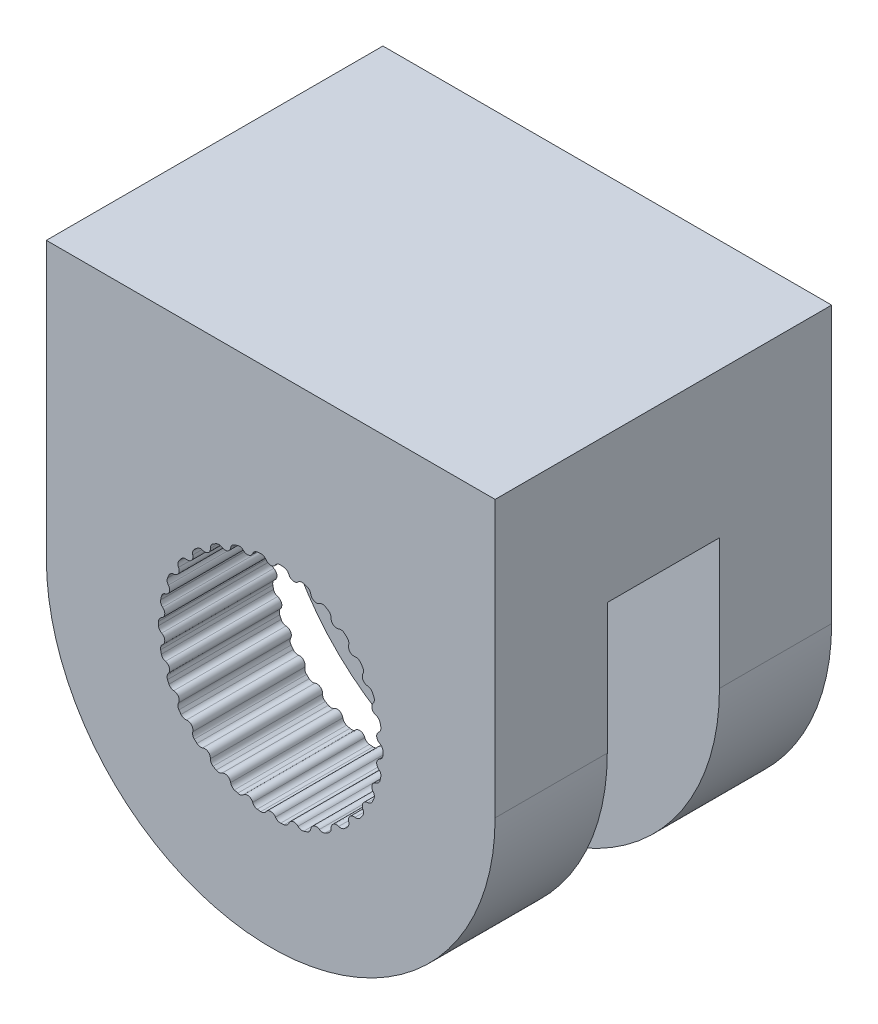
SolidWorks part; units mm, degrees
ref_plane "Front Plane" through (0, 0, 0) normal (0, 0, 1) x (1, 0, 0)
ref_plane "Top Plane" through (0, 0, 0) normal (0, 1, 0) x (1, 0, 0)
ref_plane "Right Plane" through (0, 0, 0) normal (1, 0, 0) x (0, 0, -1)
sketch "Sketch1" plane through (0, 0, 0) normal (0, 0, 1) x (1, 0, 0)
  line L0 (-51.514, -77.6376) -> (-11.514, -77.6376)
  line L1 (-51.514, -102.226) -> (-51.514, -77.6376)
  line L2 (-11.514, -102.226) -> (-11.514, -77.6376)
  arc A0 (-34.4531, -111.7843) -> (-34.7544, -111.6864) centre (-31.514, -102.226) cw
  arc A1 (-36.3762, -110.9643) -> (-36.6505, -110.806) centre (-31.514, -102.226) cw
  arc A2 (-38.0868, -109.7625) -> (-38.3221, -109.5505) centre (-31.514, -102.226) cw
  arc A3 (-39.51, -108.2312) -> (-39.6962, -107.975) centre (-31.514, -102.226) cw
  arc A4 (-40.5839, -106.4375) -> (-40.7127, -106.1482) centre (-31.514, -102.226) cw
  arc A5 (-41.2613, -104.4598) -> (-41.3272, -104.1499) centre (-31.514, -102.226) cw
  arc A6 (-41.5127, -102.3844) -> (-41.5127, -102.0676) centre (-31.514, -102.226) cw
  arc A7 (-41.3272, -100.302) -> (-41.2613, -99.9922) centre (-31.514, -102.226) cw
  arc A8 (-40.7127, -98.3038) -> (-40.5839, -98.0144) centre (-31.514, -102.226) cw
  arc A9 (-39.6962, -96.477) -> (-39.51, -96.2207) centre (-31.514, -102.226) cw
  arc A10 (-38.3221, -94.9014) -> (-38.0868, -94.6895) centre (-31.514, -102.226) cw
  arc A11 (-36.6505, -93.646) -> (-36.3762, -93.4876) centre (-31.514, -102.226) cw
  arc A12 (-34.7544, -92.7656) -> (-34.4531, -92.6677) centre (-31.514, -102.226) cw
  arc A13 (-32.7166, -92.2986) -> (-32.4016, -92.2655) centre (-31.514, -102.226) cw
  arc A14 (-30.6263, -92.2655) -> (-30.3113, -92.2986) centre (-31.514, -102.226) cw
  arc A15 (-28.5748, -92.6677) -> (-28.2736, -92.7656) centre (-31.514, -102.226) cw
  arc A16 (-26.6518, -93.4876) -> (-26.3775, -93.646) centre (-31.514, -102.226) cw
  arc A17 (-24.9412, -94.6895) -> (-24.7058, -94.9014) centre (-31.514, -102.226) cw
  arc A18 (-23.5179, -96.2207) -> (-23.3317, -96.477) centre (-31.514, -102.226) cw
  arc A19 (-22.4441, -98.0144) -> (-22.3153, -98.3038) centre (-31.514, -102.226) cw
  arc A20 (-21.7667, -99.9922) -> (-21.7008, -100.302) centre (-31.514, -102.226) cw
  arc A21 (-21.5152, -102.0676) -> (-21.5152, -102.3844) centre (-31.514, -102.226) cw
  arc A22 (-21.7008, -104.1499) -> (-21.7667, -104.4598) centre (-31.514, -102.226) cw
  arc A23 (-22.3153, -106.1482) -> (-22.4441, -106.4375) centre (-31.514, -102.226) cw
  arc A24 (-23.3317, -107.975) -> (-23.5179, -108.2312) centre (-31.514, -102.226) cw
  arc A25 (-24.7058, -109.5505) -> (-24.9412, -109.7625) centre (-31.514, -102.226) cw
  arc A26 (-26.3775, -110.806) -> (-26.6518, -110.9643) centre (-31.514, -102.226) cw
  arc A27 (-28.2736, -111.6864) -> (-28.5748, -111.7843) centre (-31.514, -102.226) cw
  arc A28 (-30.3113, -112.1534) -> (-30.6263, -112.1865) centre (-31.514, -102.226) cw
  arc A29 (-33.9496, -111.6569) -> (-33.1248, -111.8322) centre (-33.5931, -112.0075) cw
  arc A30 (-35.8572, -110.9444) -> (-35.0869, -111.2874) centre (-35.5813, -111.3614) cw
  arc A31 (-37.575, -109.8509) -> (-36.8928, -110.3466) centre (-37.3918, -110.3162) cw
  arc A32 (-39.0278, -108.4241) -> (-38.4636, -109.0508) centre (-38.9454, -108.9173) cw
  arc A33 (-40.1523, -106.7265) -> (-39.7307, -107.4568) centre (-40.1742, -107.226) cw
  arc A34 (-40.8992, -104.8321) -> (-40.6387, -105.6341) centre (-41.0245, -105.3162) cw
  arc A35 (-41.236, -102.8239) -> (-41.1479, -103.6625) centre (-41.4592, -103.2713) cw
  arc A36 (-41.1479, -100.7895) -> (-41.236, -101.6281) centre (-41.4592, -101.1807) cw
  arc A37 (-40.6387, -98.8179) -> (-40.8992, -99.6199) centre (-41.0245, -99.1358) cw
  arc A38 (-39.7307, -96.9952) -> (-40.1523, -97.7255) centre (-40.1742, -97.226) cw
  arc A39 (-38.4636, -95.4012) -> (-39.0278, -96.0278) centre (-38.9454, -95.5347) cw
  arc A40 (-36.8928, -94.1054) -> (-37.575, -94.6011) centre (-37.3918, -94.1358) cw
  arc A41 (-35.0869, -93.1646) -> (-35.8572, -93.5075) centre (-35.5813, -93.0905) cw
  arc A42 (-33.1248, -92.6197) -> (-33.9496, -92.795) centre (-33.5931, -92.4445) cw
  arc A43 (-31.0924, -92.4947) -> (-31.9356, -92.4947) centre (-31.514, -92.226) cw
  arc A44 (-29.0783, -92.795) -> (-29.9032, -92.6197) centre (-29.4349, -92.4445) cw
  arc A45 (-27.1707, -93.5075) -> (-27.9411, -93.1646) centre (-27.4466, -93.0905) cw
  arc A46 (-25.453, -94.6011) -> (-26.1352, -94.1054) centre (-25.6361, -94.1358) cw
  arc A47 (-24.0001, -96.0278) -> (-24.5644, -95.4012) centre (-24.0825, -95.5347) cw
  arc A48 (-22.8757, -97.7255) -> (-23.2973, -96.9952) centre (-22.8537, -97.226) cw
  arc A49 (-22.1287, -99.6199) -> (-22.3893, -98.8179) centre (-22.0034, -99.1358) cw
  arc A50 (-21.792, -101.6281) -> (-21.8801, -100.7895) centre (-21.5688, -101.1807) cw
  arc A51 (-21.8801, -103.6625) -> (-21.792, -102.8239) centre (-21.5688, -103.2713) cw
  arc A52 (-22.3893, -105.6341) -> (-22.1287, -104.8321) centre (-22.0034, -105.3162) cw
  arc A53 (-23.2973, -107.4568) -> (-22.8757, -106.7265) centre (-22.8537, -107.226) cw
  arc A54 (-24.5644, -109.0508) -> (-24.0001, -108.4241) centre (-24.0825, -108.9173) cw
  arc A55 (-26.1352, -110.3466) -> (-25.453, -109.8509) centre (-25.6361, -110.3162) cw
  arc A56 (-27.9411, -111.2874) -> (-27.1707, -110.9444) centre (-27.4466, -111.3614) cw
  arc A57 (-29.9032, -111.8322) -> (-29.0783, -111.6569) centre (-29.4349, -112.0075) cw
  arc A58 (-31.9356, -111.9572) -> (-31.0924, -111.9572) centre (-31.514, -112.226) cw
  arc A59 (-32.4016, -112.1865) -> (-32.7166, -112.1534) centre (-31.514, -102.226) cw
  arc A60 (-11.514, -102.226) -> (-51.514, -102.226) centre (-31.514, -102.226) cw
  arc A61 (-26.6518, -110.9643) -> (-27.1707, -110.9444) centre (-26.8949, -110.5274) cw
  arc A62 (-26.3775, -110.806) -> (-26.1352, -110.3466) centre (-26.6343, -110.377) ccw
  arc A63 (-24.9412, -109.7625) -> (-25.453, -109.8509) centre (-25.2698, -109.3856) cw
  arc A64 (-24.7058, -109.5505) -> (-24.5644, -109.0508) centre (-25.0462, -109.1843) ccw
  arc A65 (-23.5179, -108.2312) -> (-24.0001, -108.4241) centre (-23.9177, -107.931) cw
  arc A66 (-23.3317, -107.975) -> (-23.2973, -107.4568) centre (-23.7408, -107.6875) ccw
  arc A67 (-22.4441, -106.4375) -> (-22.8757, -106.7265) centre (-22.8976, -106.2269) cw
  arc A68 (-22.3153, -106.1482) -> (-22.3893, -105.6341) centre (-22.7752, -105.952) ccw
  arc A69 (-21.7667, -104.4598) -> (-22.1287, -104.8321) centre (-22.254, -104.3481) cw
  arc A70 (-21.7008, -104.1499) -> (-21.8801, -103.6625) centre (-22.1915, -104.0537) ccw
  arc A71 (-21.5152, -102.3844) -> (-21.792, -102.8239) centre (-22.0152, -102.3764) cw
  arc A72 (-21.5152, -102.0676) -> (-21.792, -101.6281) centre (-22.0152, -102.0755) ccw
  arc A73 (-21.7008, -100.302) -> (-21.8801, -100.7895) centre (-22.1915, -100.3982) cw
  arc A74 (-21.7667, -99.9922) -> (-22.1287, -99.6199) centre (-22.254, -100.1039) ccw
  arc A75 (-22.3153, -98.3038) -> (-22.3893, -98.8179) centre (-22.7752, -98.4999) cw
  arc A76 (-22.4441, -98.0144) -> (-22.8757, -97.7255) centre (-22.8976, -98.225) ccw
  arc A77 (-23.3317, -96.477) -> (-23.2973, -96.9952) centre (-23.7408, -96.7644) cw
  arc A78 (-23.5179, -96.2207) -> (-24.0001, -96.0278) centre (-23.9177, -96.521) ccw
  arc A79 (-24.7058, -94.9014) -> (-24.5644, -95.4012) centre (-25.0462, -95.2677) cw
  arc A80 (-24.9412, -94.6895) -> (-25.453, -94.6011) centre (-25.2698, -95.0663) ccw
  arc A81 (-26.3775, -93.646) -> (-26.1352, -94.1054) centre (-26.6343, -94.075) cw
  arc A82 (-26.6518, -93.4876) -> (-27.1707, -93.5075) centre (-26.8949, -93.9245) ccw
  arc A83 (-28.2736, -92.7656) -> (-27.9411, -93.1646) centre (-28.4356, -93.2386) cw
  arc A84 (-28.5748, -92.6677) -> (-29.0783, -92.795) centre (-28.7218, -93.1456) ccw
  arc A85 (-29.9032, -92.6197) -> (-30.3113, -92.2986) centre (-30.3715, -92.7949) ccw
  arc A86 (-30.6263, -92.2655) -> (-31.0924, -92.4947) centre (-30.6707, -92.7635) ccw
  arc A87 (-28.5748, -111.7843) -> (-29.0783, -111.6569) centre (-28.7218, -111.3064) cw
  arc A88 (-28.2736, -111.6864) -> (-27.9411, -111.2874) centre (-28.4356, -111.2134) ccw
  arc A89 (-32.4016, -92.2655) -> (-31.9356, -92.4947) centre (-32.3572, -92.7635) cw
  arc A90 (-32.7166, -92.2986) -> (-33.1248, -92.6197) centre (-32.6565, -92.7949) ccw
  arc A91 (-34.4531, -92.6677) -> (-33.9496, -92.795) centre (-34.3062, -93.1456) cw
  arc A92 (-34.7544, -92.7656) -> (-35.0869, -93.1646) centre (-34.5924, -93.2386) ccw
  arc A93 (-36.3762, -93.4876) -> (-35.8572, -93.5075) centre (-36.1331, -93.9245) cw
  arc A94 (-36.6505, -93.646) -> (-36.8928, -94.1054) centre (-36.3937, -94.075) ccw
  arc A95 (-38.0868, -94.6895) -> (-37.575, -94.6011) centre (-37.7581, -95.0663) cw
  arc A96 (-38.3221, -94.9014) -> (-38.4636, -95.4012) centre (-37.9817, -95.2677) ccw
  arc A97 (-39.51, -96.2207) -> (-39.0278, -96.0278) centre (-39.1102, -96.521) cw
  arc A98 (-39.6962, -96.477) -> (-39.7307, -96.9952) centre (-39.2871, -96.7644) ccw
  arc A99 (-40.5839, -98.0144) -> (-40.1523, -97.7255) centre (-40.1304, -98.225) cw
  arc A100 (-40.7127, -98.3038) -> (-40.6387, -98.8179) centre (-40.2528, -98.4999) ccw
  arc A101 (-41.2613, -99.9922) -> (-40.8992, -99.6199) centre (-40.7739, -100.1039) cw
  arc A102 (-41.3272, -100.302) -> (-41.1479, -100.7895) centre (-40.8365, -100.3982) ccw
  arc A103 (-41.5127, -102.0676) -> (-41.236, -101.6281) centre (-41.0128, -102.0755) cw
  arc A104 (-41.5127, -102.3844) -> (-41.236, -102.8239) centre (-41.0128, -102.3764) ccw
  arc A105 (-41.3272, -104.1499) -> (-41.1479, -103.6625) centre (-40.8365, -104.0537) cw
  arc A106 (-41.2613, -104.4598) -> (-40.8992, -104.8321) centre (-40.7739, -104.3481) ccw
  arc A107 (-40.7127, -106.1482) -> (-40.6387, -105.6341) centre (-40.2528, -105.952) cw
  arc A108 (-40.5839, -106.4375) -> (-40.1523, -106.7265) centre (-40.1304, -106.2269) ccw
  arc A109 (-39.6962, -107.975) -> (-39.7307, -107.4568) centre (-39.2871, -107.6875) cw
  arc A110 (-39.51, -108.2312) -> (-39.0278, -108.4241) centre (-39.1102, -107.931) ccw
  arc A111 (-38.3221, -109.5505) -> (-38.4636, -109.0508) centre (-37.9817, -109.1843) cw
  arc A112 (-38.0868, -109.7625) -> (-37.575, -109.8509) centre (-37.7581, -109.3856) ccw
  arc A113 (-36.6505, -110.806) -> (-36.8928, -110.3466) centre (-36.3937, -110.377) cw
  arc A114 (-36.3762, -110.9643) -> (-35.8572, -110.9444) centre (-36.1331, -110.5274) ccw
  arc A115 (-34.7544, -111.6864) -> (-35.0869, -111.2874) centre (-34.5924, -111.2134) cw
  arc A116 (-34.4531, -111.7843) -> (-33.9496, -111.6569) centre (-34.3062, -111.3064) ccw
  arc A117 (-33.1248, -111.8322) -> (-32.7166, -112.1534) centre (-32.6565, -111.657) ccw
  arc A118 (-31.9356, -111.9572) -> (-32.4016, -112.1865) centre (-32.3572, -111.6885) cw
  arc A119 (-30.6263, -112.1865) -> (-31.0924, -111.9572) centre (-30.6707, -111.6885) cw
  arc A120 (-30.3113, -112.1534) -> (-29.9032, -111.8322) centre (-30.3715, -111.657) ccw
  point P4 (-51.514, -89.9318)
  point P6 (-11.514, -89.9318)
  point P99 (-31.514, -102.226)
  dimension "D1" = 0.5
  dimension "D2" = 0.5
  dimension "D3" = 0.5
  dimension "D4" = 0.5
  dimension "D5" = 0.5
  dimension "D6" = 0.5
  dimension "D7" = 0.5
  dimension "D8" = 0.5
  dimension "D9" = 0.5
  dimension "D10" = 0.5
  dimension "D11" = 0.5
  dimension "D12" = 0.5
  dimension "D13" = 0.5
  dimension "D14" = 0.5
  dimension "D15" = 0.5
  dimension "D16" = 0.5
  dimension "D17" = 0.5
  dimension "D18" = 0.5
  dimension "D19" = 0.5
  dimension "D20" = 0.5
  dimension "D21" = 0.5
  dimension "D22" = 0.5
  dimension "D23" = 0.5
  dimension "D24" = 0.5
  dimension "D25" = 0.5
  dimension "D26" = 0.5
  dimension "D27" = 0.5
  dimension "D28" = 0.5
  dimension "D29" = 0.5
  dimension "D30" = 0.5
  dimension "D31" = 0.5
  dimension "D32" = 0.5
  dimension "D33" = 0.5
  dimension "D34" = 0.5
  dimension "D35" = 0.5
  dimension "D36" = 0.5
  dimension "D37" = 0.5
  dimension "D38" = 0.5
  dimension "D39" = 0.5
  dimension "D40" = 0.5
  dimension "D41" = 0.5
  dimension "D42" = 0.5
  dimension "D43" = 0.5
  dimension "D44" = 0.5
  dimension "D45" = 0.5
  dimension "D46" = 0.5
  dimension "D47" = 0.5
  dimension "D48" = 0.5
  dimension "D49" = 0.5
  dimension "D50" = 0.5
  dimension "D51" = 0.5
  dimension "D52" = 0.5
  dimension "D53" = 0.5
  dimension "D54" = 0.5
  dimension "D55" = 0.5
  dimension "D56" = 0.5
  dimension "D57" = 0.5
  dimension "D58" = 0.5
  dimension "D59" = 0.5
  dimension "D60" = 0.5
extrude "Boss-Extrude1" add sketch "Sketch1" along normal blind 10
sketch "Sketch2" plane through (0, 0, 0) normal (0, 0, -1) x (-1, 0, 0)
  line L6 (51.514, -102.226) -> (51.514, -77.6376)
  line L7 (51.514, -77.6376) -> (11.514, -77.6376)
  line L8 (11.514, -77.6376) -> (11.514, -102.226)
  line L9 (51.514, -102.226) -> (51.514, -77.6376)
  line L10 (51.514, -77.6376) -> (11.514, -77.6376)
  line L11 (11.514, -77.6376) -> (11.514, -102.226)
  arc A2 (11.514, -102.226) -> (51.514, -102.226) centre (31.514, -102.226) ccw
  arc A3 (11.514, -102.226) -> (51.514, -102.226) centre (31.514, -102.226) ccw
  dimension "D1" = 0
extrude "Boss-Extrude2" add sketch "Sketch2" along normal blind 20
sketch "Sketch3" plane through (-51.514, 0, 0) normal (-1, 0, 0) x (0, 0, 1)
  line L0 (0, -92.2986) -> (0, -90.6004)
  line L2 (0, -92.2986) -> (0, -122.226)
  line L3 (-20, -122.226) -> (10, -122.226) construction
  line L4 (-10, -122.226) -> (-10, -90.6004)
  line L6 (-10, -122.226) -> (0, -122.226)
  line L7 (-10, -90.6004) -> (0, -90.6004)
  dimension "D1" = 10
extrude "Cut-Extrude1" cut sketch "Sketch3" against normal blind 60 and the other way through all
sketch "Sketch4" plane through (0, 0, 0) normal (0, 0, -1) x (-1, 0, 0)
  circle A0 centre (31.514, -102.226) radius 20
extrude "Cut-Extrude2" cut sketch "Sketch4" along normal blind 10
